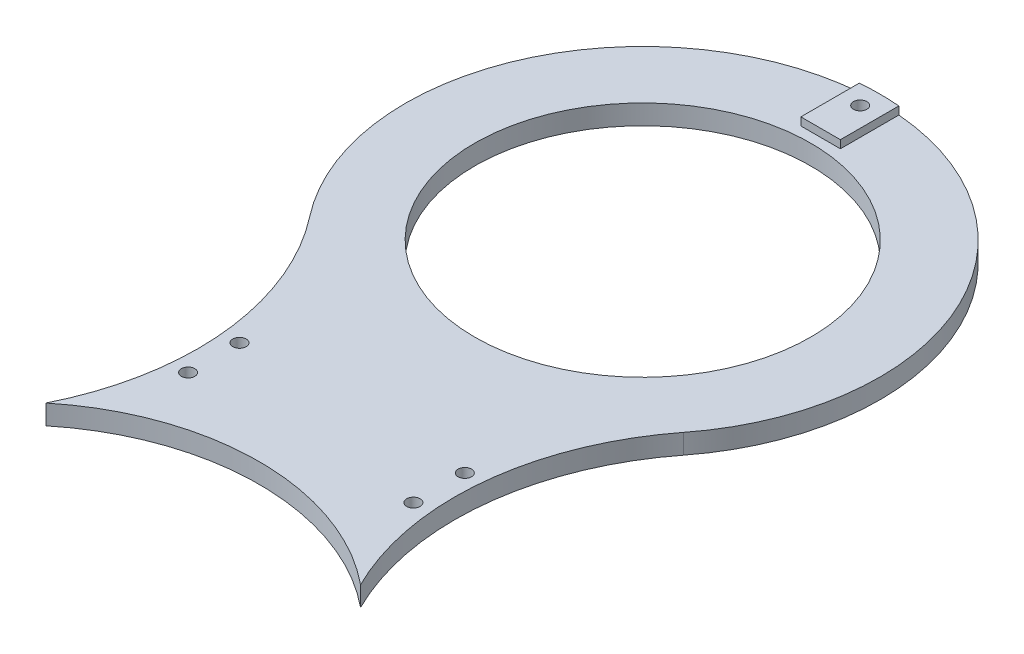
SolidWorks part; units mm, degrees
material "PLA"
ref_plane "Alzado" through (0, 0, 0) normal (0, 0, 1) x (1, 0, 0)
ref_plane "Planta" through (0, 0, 0) normal (0, 1, 0) x (1, 0, 0)
ref_plane "Vista lateral" through (0, 0, 0) normal (1, 0, 0) x (0, 0, -1)
sketch "Croquis1" plane through (0, 0, 0) normal (0, 1, 0) x (1, 0, 0)
  arc A0 (39.7829, 48.85) -> (-39.7829, 48.85) centre (0, 0) ccw
  circle A1 centre (0, 160) radius 42.5
  arc A2 (47.2938, 123.0771) -> (-47.2938, 123.0771) centre (0, 160) ccw
  arc A3 (-39.7829, 48.85) -> (-47.2938, 123.0771) centre (-102.4698, 80.0004) ccw
  arc A4 (47.2938, 123.0771) -> (39.7829, 48.85) centre (102.4698, 80.0004) ccw
  dimension "D2" = 120
  dimension "D3" = 85
  dimension "D4" = 126
  dimension "D5" = 140
  dimension "D1" = 160
  dimension "D6" = 48.85
extrude "Saliente-Extruir1" add sketch "Croquis1" along normal blind 5
sketch "Croquis2" plane through (0, 5, 0) normal (0, 1, 0) x (1, 0, 0)
  line L1 (5, 205) -> (-5, 205)
  line L2 (5, 205) -> (5, 219.7913)
  line L4 (-5, 205) -> (-5, 219.7913)
  arc A0 (5, 219.7913) -> (-5, 219.7913) centre (0, 160) ccw
  arc A1 (47.2938, 123.0771) -> (-47.2938, 123.0771) centre (0, 160) ccw construction
  point P6 (0, 205)
  dimension "D1" = 10
  dimension "D2" = 45
extrude "Saliente-Extruir2" add sketch "Croquis2" along normal blind 2
sketch "Croquis3" plane through (0, 7, 0) normal (0, 1, 0) x (1, 0, 0)
  line L1 (28.5, 73.5) -> (-28.5, 73.5) construction
  line L2 (28.5, 73.5) -> (28.5, 86.5) construction
  line L3 (28.5, 86.5) -> (-28.5, 86.5) construction
  line L4 (-28.5, 73.5) -> (-28.5, 86.5) construction
  line L5 (28.5, 73.5) -> (-28.5, 86.5) construction
  line L6 (28.5, 86.5) -> (-28.5, 73.5) construction
  circle A0 centre (0, 215) radius 1.7
  circle A1 centre (-28.5, 86.5) radius 1.7
  circle A2 centre (-28.5, 73.5) radius 1.7
  circle A3 centre (28.5, 73.5) radius 1.7
  circle A4 centre (28.5, 86.5) radius 1.7
  circle A5 centre (0, 160) radius 42.5 construction
  point P2 (0, 80)
  dimension "D3" = 3.4
  dimension "D1" = 13
  dimension "D2" = 57
  dimension "D4" = 55
  dimension "D5" = 73.5
extrude "Cortar-Extruir1" cut sketch "Croquis3" against normal blind 21
sketch "Croquis4" plane through (0, 0, 0) normal (0, -1, 0) x (1, 0, 0)
  circle A0 centre (0, -215) radius 2.95
  dimension "D1" = 5.9
extrude "Cortar-Extruir2" cut sketch "Croquis4" against normal blind 3
